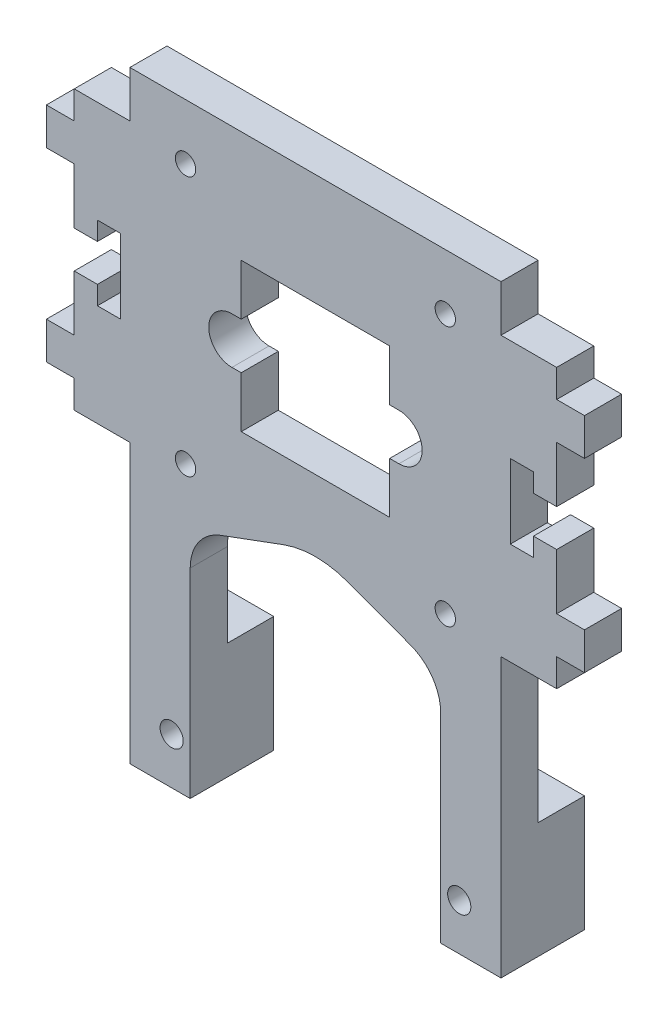
SolidWorks part; units mm, degrees
material "自定义塑料"
ref_plane "前视基准面" through (0, 0, 0) normal (0, 0, 1) x (1, 0, 0)
ref_plane "上视基准面" through (0, 0, 0) normal (0, 1, 0) x (1, 0, 0)
ref_plane "右视基准面" through (0, 0, 0) normal (1, 0, 0) x (0, 0, -1)
sketch "草图1" plane through (0, 0, 0) normal (0, 0, 1) x (1, 0, 0)
  line L1 (-29, -15) -> (29, -15)
  line L2 (-29, -15) -> (-29, 15)
  line L3 (-29, 15) -> (29, 15)
  line L4 (29, -15) -> (29, 15)
  line L5 (-29, -15) -> (29, 15) construction
  line L6 (-29, 15) -> (29, -15) construction
  point P0 (0, 0)
  dimension "D1" = 58
  dimension "D2" = 30
extrude "凸台-拉伸1" add sketch "草图1" along normal blind 4
sketch "草图2" plane through (29, 0, 0) normal (1, 0, 0) x (0, 0, -1)
  line L0 (-4, -15) -> (-4, 15) construction
  line L1 (-4, 12) -> (0, 12)
  line L2 (-4, 12) -> (-4, 8)
  line L3 (-4, 8) -> (0, 8)
  line L4 (0, 12) -> (0, 8)
  line L5 (0, -15) -> (0, 15) construction
  line L6 (-4, 15) -> (0, 15) construction
  line L7 (-4, 2) -> (0, 2)
  line L8 (-4, 2) -> (-4, -2)
  line L9 (-4, -2) -> (0, -2)
  line L10 (0, 2) -> (0, -2)
  line L12 (-4, -8) -> (0, -8)
  line L13 (-4, -8) -> (-4, -12)
  line L14 (-4, -12) -> (0, -12)
  line L15 (0, -8) -> (0, -12)
  line L16 (-4, 15) -> (0, 15)
  line L17 (-4, 15) -> (-4, -15)
  line L18 (-4, -15) -> (0, -15)
  line L19 (0, 15) -> (0, -15)
  line M10 (0, -15) -> (0, 15)
  line M11 (0, 15) -> (-4, 15)
  line M12 (-4, 15) -> (-4, -15)
  line M13 (-4, -15) -> (0, -15)
  dimension "D1" = 4
  dimension "D2" = 4
  dimension "D3" = 3
  dimension "D4" = 6
  dimension "D5" = 4
  dimension "D6" = 6
extrude "切除-拉伸2" cut sketch "草图2" against normal blind 3 contours L1 M12 M10 M11 | L7 L3 M12 M10 | L9 L7 M12 M10 | L12 L9 M12 M10 | L14 M12 M13 M10
sketch "草图3" plane through (-29, 0, 0) normal (-1, 0, 0) x (0, 0, 1)
  line L0 (0, 15) -> (0, -15) construction
  line L1 (0, 12) -> (4, 12)
  line L2 (0, 12) -> (0, 8)
  line L3 (0, 8) -> (4, 8)
  line L4 (4, 12) -> (4, 8)
  line L5 (4, 15) -> (4, -15) construction
  line L6 (4, 15) -> (0, 15) construction
  line L7 (0, -8) -> (4, -8)
  line L8 (0, -8) -> (0, -12)
  line L9 (0, -12) -> (4, -12)
  line L10 (4, -8) -> (4, -12)
  line L11 (0, 2) -> (4, 2)
  line L12 (0, 2) -> (0, -2)
  line L13 (0, -2) -> (4, -2)
  line L14 (4, 2) -> (4, -2)
  line L16 (0, 15) -> (4, 15)
  line L17 (0, 15) -> (0, -15)
  line L18 (0, -15) -> (4, -15)
  line L19 (4, 15) -> (4, -15)
  line M12 (0, 15) -> (0, -15)
  line M13 (0, -15) -> (4, -15)
  line M14 (4, -15) -> (4, 15)
  line M15 (4, 15) -> (0, 15)
  dimension "D1" = 3
  dimension "D2" = 4
  dimension "D3" = 6
  dimension "D4" = 4
  dimension "D5" = 6
  dimension "D6" = 4
extrude "切除-拉伸3" cut sketch "草图3" against normal blind 3 contours L1 M12 M14 M15 | L11 L3 M12 M14 | L13 L11 M12 M14 | L13 L7 M12 M14 | L9 M12 M13 M14
sketch "草图4" plane through (0, 0, 0) normal (0, 0, -1) x (-1, 0, 0)
  line L0 (-26, 2) -> (-23.5, 2)
  line L1 (-26, -8) -> (-26, 8) construction
  line L2 (-23.5, 2) -> (-23.5, 4)
  line L3 (-23.5, 4) -> (-21, 4)
  line L4 (-21, 4) -> (-21, -4)
  line L5 (-21, -4) -> (-23.5, -4)
  line L6 (-23.5, -4) -> (-23.5, -2)
  line L7 (-23.5, -2) -> (-26, -2)
  line L8 (-26, -2) -> (-26, 2)
  line L9 (0, 0) -> (-37.8887, 0) construction
  line L10 (-37.8887, 0) -> (32.9924, 0) construction
  line L11 (26, -2) -> (23.5, -2)
  line L12 (26, 8) -> (26, -8) construction
  line L13 (23.5, -2) -> (23.5, -4)
  line L14 (23.5, -4) -> (21, -4)
  line L15 (21, -4) -> (21, 4)
  line L16 (21, 4) -> (23.5, 4)
  line L17 (23.5, 4) -> (23.5, 2)
  line L18 (23.5, 2) -> (26, 2)
  line L19 (26, 2) -> (26, -2)
  dimension "D1" = 8
  dimension "D2" = 2.5
  dimension "D3" = 2.5
  dimension "D4" = 4
  dimension "D5" = 2
  dimension "D6" = 4
  dimension "D7" = 4
  dimension "D8" = 2
  dimension "D9" = 8
  dimension "D10" = 4
  dimension "D11" = 2.5
  dimension "D12" = 2.5
  dimension "D13" = 2.5
extrude "切除-拉伸4" cut sketch "草图4" against normal through all
sketch "草图5" plane through (0, 0, 0) normal (0, 0, -1) x (-1, 0, 0)
  line L0 (-9, 0) -> (9, 0) construction
  line L1 (-9, 2.5) -> (9, 2.5)
  line L2 (-9, -2.5) -> (9, -2.5)
  circle A0 centre (0, 0) radius 7.5
  arc A1 (-9, 2.5) -> (-9, -2.5) centre (-9, 0) ccw
  arc A2 (9, -2.5) -> (9, 2.5) centre (9, 0) ccw
  point P5 (0, 0)
  dimension "D1" = 15
  dimension "D3" = 2.5
  dimension "D2" = 18
  dimension "D4" = 9
extrude "切除-拉伸5" cut sketch "草图5" against normal through all
sketch "草图11" plane through (0, 0, 4) normal (0, 0, 1) x (1, 0, 0)
  line L1 (-8, -8) -> (8, -8)
  line L2 (-8, -8) -> (-8, 8)
  line L3 (-8, 8) -> (8, 8)
  line L4 (8, -8) -> (8, 8)
  line L5 (-8, -8) -> (8, 8) construction
  line L6 (-8, 8) -> (8, -8) construction
  point P0 (0, 0)
  dimension "D1" = 16
extrude "切除-拉伸10" cut sketch "草图11" against normal blind 10
sketch "草图12" plane through (0, 0, 0) normal (0, 0, -1) x (-1, 0, 0)
  line L0 (-26, 15) -> (26, 15) construction
  line L1 (-20, 20) -> (20, 20)
  line L2 (-20, 20) -> (-20, 15)
  line L3 (-20, 15) -> (20, 15)
  line L4 (20, 20) -> (20, 15)
  line L5 (26, -15) -> (-26, -15) construction
  line L6 (-20, -15) -> (20, -15)
  line L7 (-20, -15) -> (-20, -20)
  line L8 (-20, -20) -> (20, -20)
  line L9 (20, -15) -> (20, -20)
  line L10 (0, 2.2) -> (0, -2.2) construction
  dimension "D1" = 40
  dimension "D2" = 20
  dimension "D3" = 40
  dimension "D4" = 20
  dimension "D5" = 5
  dimension "D6" = 5
extrude "凸台-拉伸2" add sketch "草图12" against normal up to surface (4 mm away) up to face at (0, 0, 4)
sketch "草图13" plane through (0, 0, 0) normal (0, 0, -1) x (-1, 0, 0)
  line L1 (14, 14) -> (-14, 14) construction
  line L2 (14, 14) -> (14, -14) construction
  line L3 (14, -14) -> (-14, -14) construction
  line L4 (-14, 14) -> (-14, -14) construction
  line L5 (14, 14) -> (-14, -14) construction
  line L6 (14, -14) -> (-14, 14) construction
  circle A0 centre (14, -14) radius 2.5
  circle A1 centre (-14, -14) radius 2.5
  circle A2 centre (14, 14) radius 2.5
  circle A3 centre (-14, 14) radius 2.5
  point P0 (0, 0)
  dimension "D3" = 5
  dimension "D4" = 5
  dimension "D5" = 5
  dimension "D6" = 5
  dimension "D1" = 28
  dimension "D2" = 28
extrude "凸台-拉伸3" add sketch "草图13" along normal blind 2.5
sketch "草图14" plane through (0, 0, -2.5) normal (0, 0, -1) x (-1, 0, 0)
  circle A0 centre (14, -14) radius 1.1
  circle A1 centre (-14, -14) radius 1.1
  circle A2 centre (-14, 14) radius 1.1
  circle A3 centre (14, 14) radius 1.1
  dimension "D1" = 2.2
extrude "切除-拉伸11" cut sketch "草图14" against normal through all
sketch "草图15" plane through (0, 0, 0) normal (0, 0, -1) x (-1, 0, 0)
  line L0 (13.5, -45) -> (13.5, -20)
  line L1 (-20, -20) -> (20, -20) construction
  line L2 (-13.5, -20) -> (-13.5, -45)
  line L3 (0, 3.575) -> (0, -3.575) construction
  line L4 (20, -20) -> (20, -45)
  line L5 (20, -45) -> (13.5, -45)
  line L6 (-20, -20) -> (-20, -45)
  line L7 (-20, -15) -> (-20, -20) construction
  line L8 (-20, -45) -> (-13.5, -45)
  line L9 (20, -20) -> (13.5, -20)
  line L10 (-13.5, -20) -> (-20, -20)
  circle A0 centre (15.5, -40) radius 1.25
  circle A1 centre (-15.5, -40) radius 1.25
  dimension "D3" = 2.5
  dimension "D4" = 2.5
  dimension "D1" = 31
  dimension "D2" = 27
  dimension "D5" = 20
  dimension "D6" = 13.5
  dimension "D7" = 15.5
  dimension "D8" = 25
  dimension "D9" = 25
extrude "凸台-拉伸4" add sketch "草图15" against normal up to surface (4 mm away) up to face at (-15.1, 14, 4)
sketch "草图16" plane through (0, 0, 0) normal (0, 0, -1) x (-1, 0, 0)
  line L0 (13.5, -20) -> (13.5, -45) construction
  line L1 (20, -45) -> (13.5, -45)
  line L2 (20, -45) -> (20, -32.5)
  line L3 (20, -32.5) -> (13.5, -32.5)
  line L4 (13.5, -45) -> (13.5, -32.5)
  line L5 (-13.5, -45) -> (-13.5, -20) construction
  line L6 (-13.5, -32.5) -> (-20, -32.5)
  line L7 (-13.5, -32.5) -> (-13.5, -45)
  line L8 (-13.5, -45) -> (-20, -45)
  line L9 (-20, -32.5) -> (-20, -45)
  circle A0 centre (15.5, -40) radius 1.25
  circle A1 centre (-15.5, -40) radius 1.25
  dimension "D1" = 2.5
  dimension "D2" = 2.5
extrude "凸台-拉伸5" add sketch "草图16" along normal blind 5
sketch "草图17" plane through (0, 0, 0) normal (0, 0, -1) x (-1, 0, 0)
  line L0 (13.5, -20) -> (0, -15)
  line L1 (0, 4.95) -> (0, -4.95) construction
  line L2 (0, -15) -> (-13.5, -20)
  line L3 (-13.5, -20) -> (13.5, -20) construction
  line L4 (13.5, -20) -> (-13.5, -20)
  dimension "D1" = 5
extrude "切除-拉伸12" cut sketch "草图17" against normal through all
fillet "圆角1" radius 10 1 edges at (0, -15, 2)
fillet "圆角2" radius 5 2 edges at (13.5, -20, 2) (-13.5, -20, 2)
